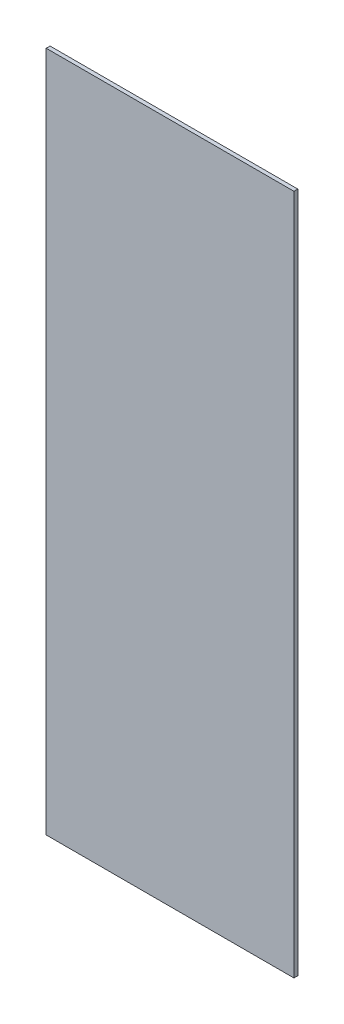
SolidWorks part; units mm, degrees
ref_plane "Front Plane" through (0, 0, 0) normal (0, 0, 1) x (1, 0, 0)
ref_plane "Top Plane" through (0, 0, 0) normal (0, 1, 0) x (1, 0, 0)
ref_plane "Right Plane" through (0, 0, 0) normal (1, 0, 0) x (0, 0, -1)
sketch "Sketch1" plane through (0, 0, 0) normal (0, 0, 1) x (1, 0, 0)
  line L1 (0, 0) -> (50.8, 0)
  line L2 (0, 0) -> (0, 139.7)
  line L3 (0, 139.7) -> (50.8, 139.7)
  line L4 (50.8, 0) -> (50.8, 139.7)
  dimension "D1" = 50.8
  dimension "D2" = 139.7
extrude "Boss-Extrude1" add sketch "Sketch1" along normal blind 0.7937
